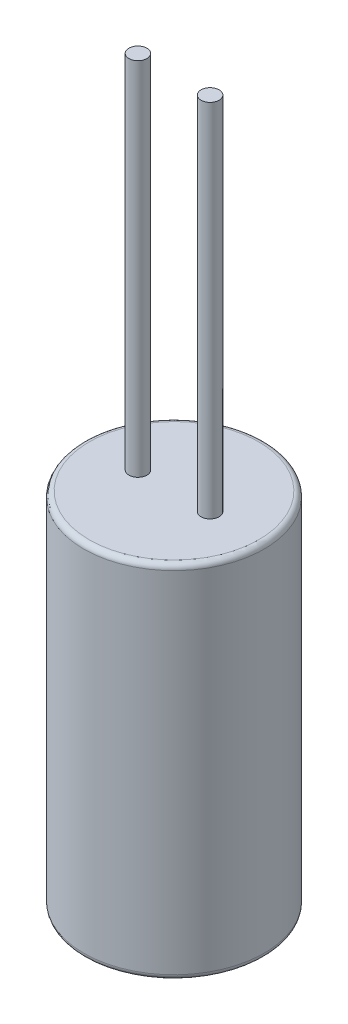
SolidWorks part; units mm, degrees
ref_plane "Front Plane" through (0, 0, 0) normal (0, 0, 1) x (1, 0, 0)
ref_plane "Top Plane" through (0, 0, 0) normal (0, 1, 0) x (1, 0, 0)
ref_plane "Right Plane" through (0, 0, 0) normal (1, 0, 0) x (0, 0, -1)
sketch "Sketch1" plane through (0, 0, 0) normal (0, 1, 0) x (1, 0, 0)
  circle A0 centre (0, 0) radius 5
  dimension "10" = 10
extrude "Boss-Extrude1" add sketch "Sketch1" along normal blind 20
sketch "Sketch2" plane through (0, 20, 0) normal (0, 1, 0) x (1, 0, 0)
  line L0 (0, 3.2589) -> (0, -3.1719) construction
  circle A0 centre (-2, 0) radius 0.5
  circle A1 centre (2, 0) radius 0.5
  point P7 (0, 0)
  dimension "D1" = 1
  dimension "D2" = 1
  dimension "D3" = 4
extrude "Boss-Extrude2" add sketch "Sketch2" along normal blind 20
fillet "Fillet1" radius 0.3 2 edges at (0, 0, 5) (0, 20, 5)
